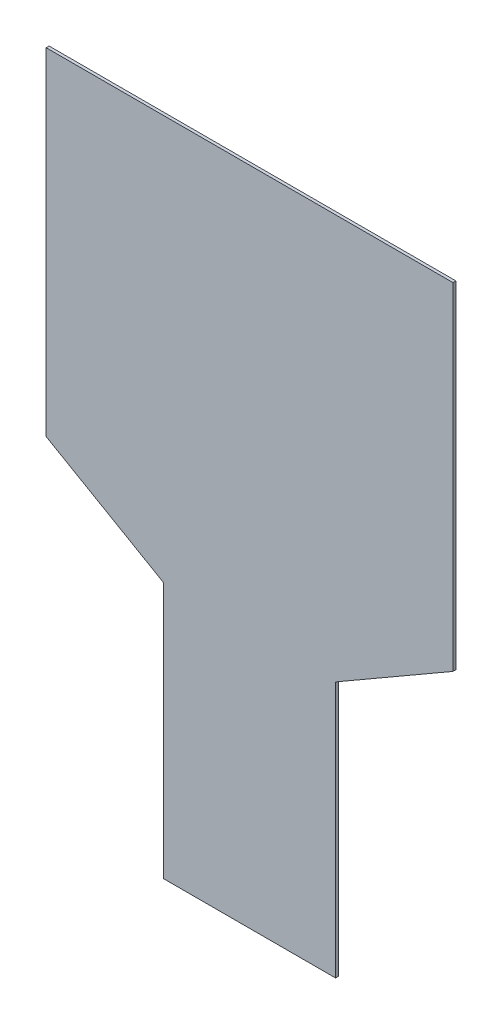
SolidWorks part; units mm, degrees
ref_plane "Plano frontal" through (0, 0, 0) normal (0, 0, 1) x (1, 0, 0)
ref_plane "Plano superior" through (0, 0, 0) normal (0, 1, 0) x (1, 0, 0)
ref_plane "Plano direito" through (0, 0, 0) normal (1, 0, 0) x (0, 0, -1)
sketch "Esboço1" plane through (0, 0, 0) normal (0, 0, 1) x (1, 0, 0)
  line L3 (2.2377, -180.1284) -> (2.2377, 169.9307) construction
  line L6 (106.2377, 175.6527) -> (-101.7623, 175.6527)
  line L7 (-101.7623, 175.6527) -> (-101.7623, 3.418)
  line L8 (-101.7623, 3.418) -> (-41.7623, -31.223)
  line L9 (-41.7623, -31.223) -> (-41.7623, -162.3473)
  line L10 (-41.7623, -162.3473) -> (46.2377, -162.3473)
  line L11 (46.2377, -31.223) -> (46.2377, -162.3473)
  line L12 (106.2377, 3.418) -> (46.2377, -31.223)
  line L13 (106.2377, 175.6527) -> (106.2377, 3.418)
extrude "Ressalto-extrusão1" add sketch "Esboço1" along normal blind 1.5
